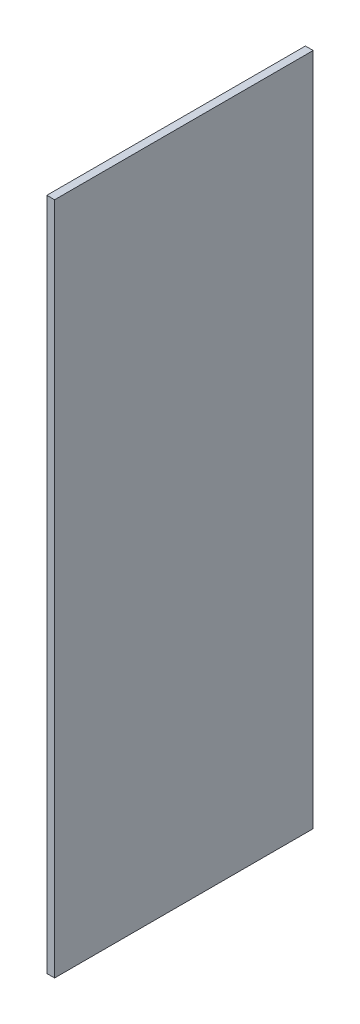
SolidWorks part; units mm, degrees
ref_plane "Спереди" through (0, 0, 0) normal (0, 0, 1) x (1, 0, 0)
ref_plane "Сверху" through (0, 0, 0) normal (0, 1, 0) x (1, 0, 0)
ref_plane "Справа" through (0, 0, 0) normal (1, 0, 0) x (0, 0, -1)
sketch "Эскиз1" plane through (0, 0, 0) normal (1, 0, 0) x (0, 0, -1)
  line L1 (0, 0) -> (600, 0)
  line L2 (0, 0) -> (0, 1564)
  line L3 (0, 1564) -> (600, 1564)
  line L4 (600, 0) -> (600, 1564)
  dimension "D1" = 600
  dimension "D2" = 1564
extrude "Бобышка-Вытянуть1" add sketch "Эскиз1" along normal blind 18
